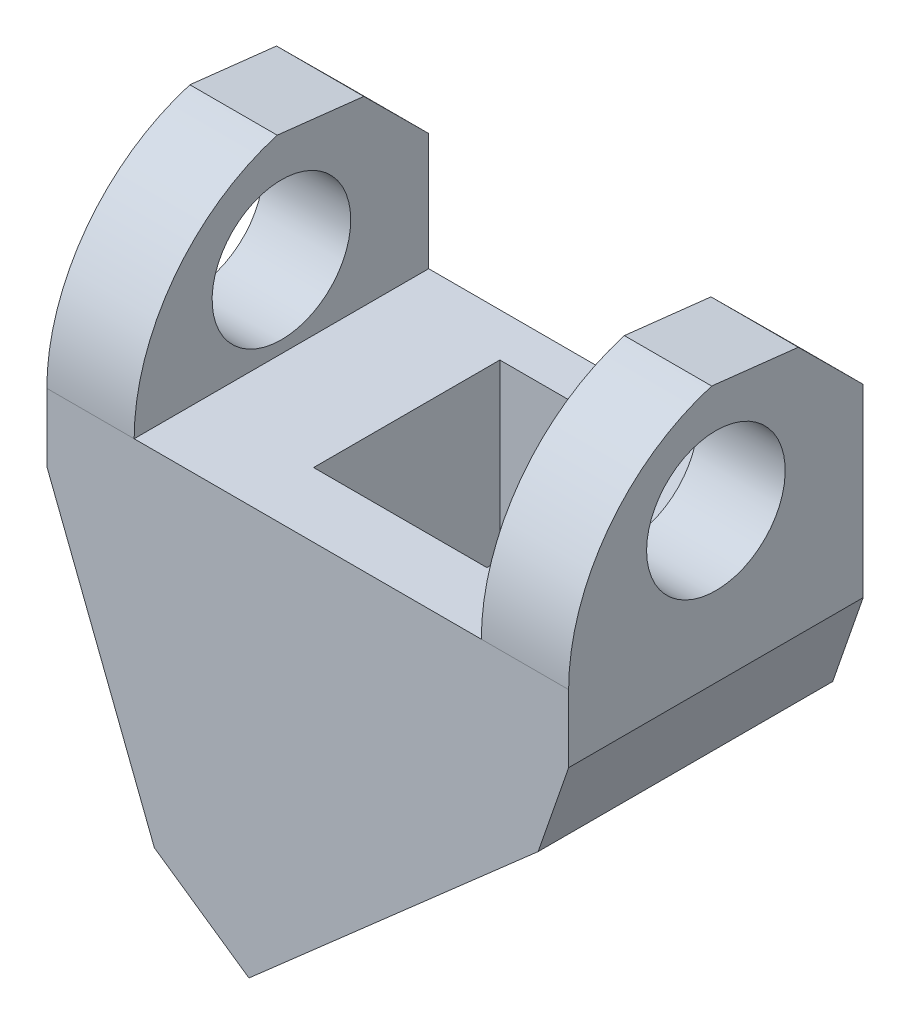
SolidWorks part; units mm, degrees
material "1060 Alloy"
ref_plane "Front Plane" through (0, 0, 0) normal (0, 0, 1) x (1, 0, 0)
ref_plane "Top Plane" through (0, 0, 0) normal (0, 1, 0) x (1, 0, 0)
ref_plane "Right Plane" through (0, 0, 0) normal (1, 0, 0) x (0, 0, -1)
sketch "Sketch1" plane through (0, 0, 0) normal (0, 0, 1) x (1, 0, 0)
  line L2 (-16.5502, 16.3894) -> (-16.5502, 1.3894)
  line L3 (-16.5502, 1.3894) -> (-10.3437, -14.5706)
  line L4 (-10.3437, -14.5706) -> (-4.884, -18.3497)
  line L5 (-4.884, -18.3497) -> (11.8091, -3.6845)
  line L6 (11.8091, -3.6845) -> (13.5679, 1.3894)
  line L7 (13.5679, 1.3894) -> (13.5679, 16.3894)
  line L8 (13.5679, 16.3894) -> (8.5279, 16.3894)
  line L9 (8.5279, 16.3894) -> (8.5279, 5.2924)
  line L10 (8.5279, 5.2924) -> (-11.5102, 5.2924)
  line L11 (-11.5102, 5.2924) -> (-11.5102, 16.3894)
  line L12 (-11.5102, 16.3894) -> (-16.5502, 16.3894)
  dimension "D2" = 5.04
  dimension "D3" = 15
  dimension "D4" = 15.96
  dimension "D5" = 6.64
  dimension "D6" = 22.22
  dimension "D7" = 158.75
  dimension "D8" = 145.94
  dimension "D9" = 104.01
  dimension "D10" = 5.37
  dimension "D12" = 15
  dimension "D13" = 11.097
  dimension "D14" = 5.04
extrude "Boss-Extrude1" add sketch "Sketch1" along normal blind 17
sketch "Sketch2" plane through (-11.5102, 0, 0) normal (1, 0, 0) x (0, 0, -1)
  line L0 (-17, 5.2924) -> (0, 5.2924)
  line L2 (0, 1.3894) -> (0, 16.3894) construction
  line L3 (0, 12.0524) -> (-3.7439, 15.7767)
  line L4 (-3.7439, 15.7767) -> (-8.7439, 16.3393)
  line L6 (0, 5.2924) -> (0, 16.3894)
  line L7 (0, 16.3894) -> (-17, 16.3894)
  line L8 (-17, 16.3894) -> (-17, 5.2924)
  arc A0 (-17, 5.2924) -> (-8.7439, 16.3393) centre (-5.4813, 5.2924) cw
  line M6 (0, 5.2924) -> (0, 16.3894)
  line M8 (-17, 16.3894) -> (-17, 5.2924)
  dimension "D1" = 6.76
  dimension "D2" = 17
  dimension "D3" = 5
  dimension "D4" = 10
  dimension "D5" = 141.57
  dimension "D6" = 134.85
extrude "Cut-Extrude1" cut sketch "Sketch2" against normal blind 15 and the other way blind 44 contours A0 L4 L3 L7 M8 M6
sketch "Sketch3" plane through (6.971, -7.9349, 0) normal (0.66, -0.7513, 0) x (0.7513, 0.66, 0)
  line L0 (-15.78, 17) -> (-15.78, 0) construction
  line L1 (-11.76, 13.26) -> (-2.29, 13.26)
  line L2 (-11.76, 13.26) -> (-11.76, 2.51)
  line L3 (-11.76, 2.51) -> (-2.29, 2.51)
  line L4 (-2.29, 13.26) -> (-2.29, 2.51)
  line L5 (-15.78, 17) -> (6.44, 17) construction
  line L6 (-11.76, 17) -> (-11.76, 0) construction
  line L7 (-15.78, 0) -> (6.44, 0) construction
  line L8 (-2.29, 17) -> (-2.29, 0) construction
  dimension "D1" = 9.47
  dimension "D2" = 10.75
  dimension "D3" = 4.02
  dimension "D4" = 3.74
ref_plane "Plane1" through (0, 0, 10) normal (0, 0, -1) x (-1, 0, 0)
sketch "Sketch4" plane through (0, 0, 10) normal (0, 0, -1) x (-1, 0, 0)
  line L0 (0.8203, -14.7797) -> (9.4908, -9.2506)
  line L3 (1.8639, -15.6965) -> (-5.2506, -9.4463) construction
  dimension "D1" = 3.57
  dimension "D2" = 5.32
sweep "Cut-Sweep1" cut profiles "Sketch3" path "Sketch4"
sketch "Sketch5" plane through (0, 5.2924, 0) normal (0, 1, 0) x (1, 0, 0)
  line L0 (-4.8921, -2.51) -> (5.1079, -2.51)
  line L1 (-4.8921, -2.51) -> (-4.8921, -13.26)
  line L2 (-4.8921, -13.26) -> (5.1079, -13.26)
  line L3 (5.1079, -2.51) -> (5.1079, -13.26)
  line L4 (-4.8921, 0) -> (-4.8921, -17) construction
  line L5 (5.1079, 0) -> (5.1079, -17) construction
  line L7 (8.5279, -17) -> (-11.5102, -17) construction
  dimension "D1" = 10
  dimension "D2" = 10.75
  dimension "D3" = 8.46
  dimension "D4" = 3.74
extrude "Cut-Extrude2" cut sketch "Sketch5" against normal up to surface (25.4347 mm away)
ref_plane "Plane2" through (-1.4912, 0, 0) normal (1, 0, 0) x (0, 0, -1)
sketch "Sketch6" plane through (-1.4912, 0, 0) normal (1, 0, 0) x (0, 0, -1)
  line L0 (-17, 1.3894) -> (0, 1.3894) construction
  line L1 (-8.5, 9.9894) -> (-8.5, 1.3894) construction
  circle A0 centre (-8.5, 9.9894) radius 4
  dimension "D2" = 8
  dimension "D1" = 8.6
extrude "Cut-Extrude3" cut sketch "Sketch6" against normal mid plane 40
